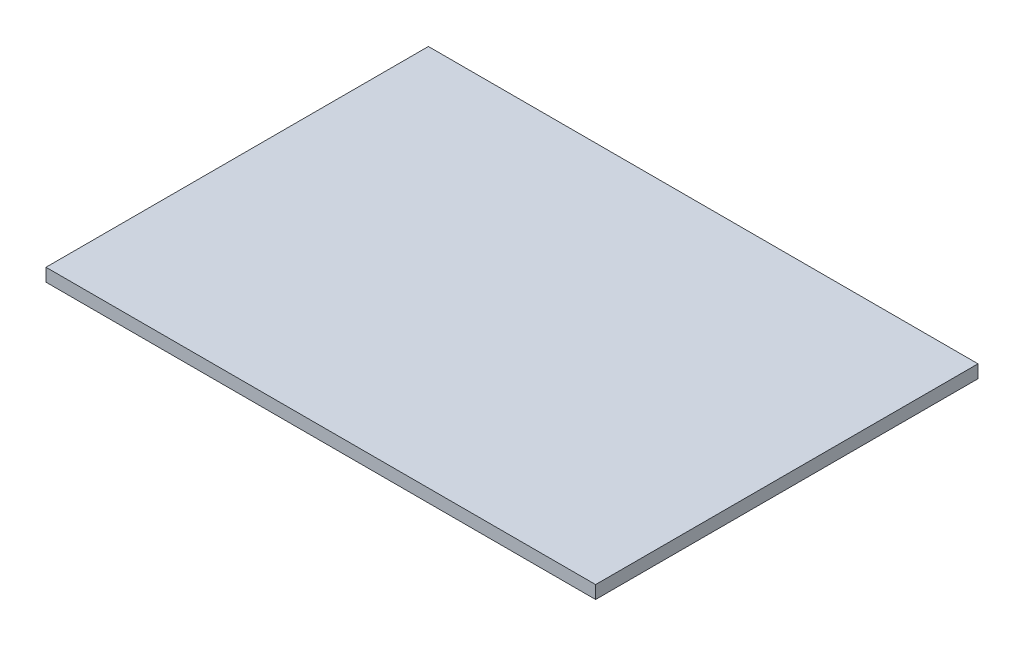
SolidWorks part; units mm, degrees
ref_plane "Front Plane" through (0, 0, 0) normal (0, 0, 1) x (1, 0, 0)
ref_plane "Top Plane" through (0, 0, 0) normal (0, 1, 0) x (1, 0, 0)
ref_plane "Right Plane" through (0, 0, 0) normal (1, 0, 0) x (0, 0, -1)
sketch "Sketch1" plane through (0, 0, 0) normal (0, 1, 0) x (1, 0, 0)
  line L1 (-212, 147.5) -> (212, 147.5)
  line L2 (-212, 147.5) -> (-212, -147.5)
  line L3 (-212, -147.5) -> (212, -147.5)
  line L4 (212, 147.5) -> (212, -147.5)
  line L5 (-212, 147.5) -> (212, -147.5) construction
  line L6 (-212, -147.5) -> (212, 147.5) construction
  point P0 (0, 0)
  dimension "D1" = 424
  dimension "D2" = 295
extrude "Boss-Extrude1" add sketch "Sketch1" against normal blind 10
